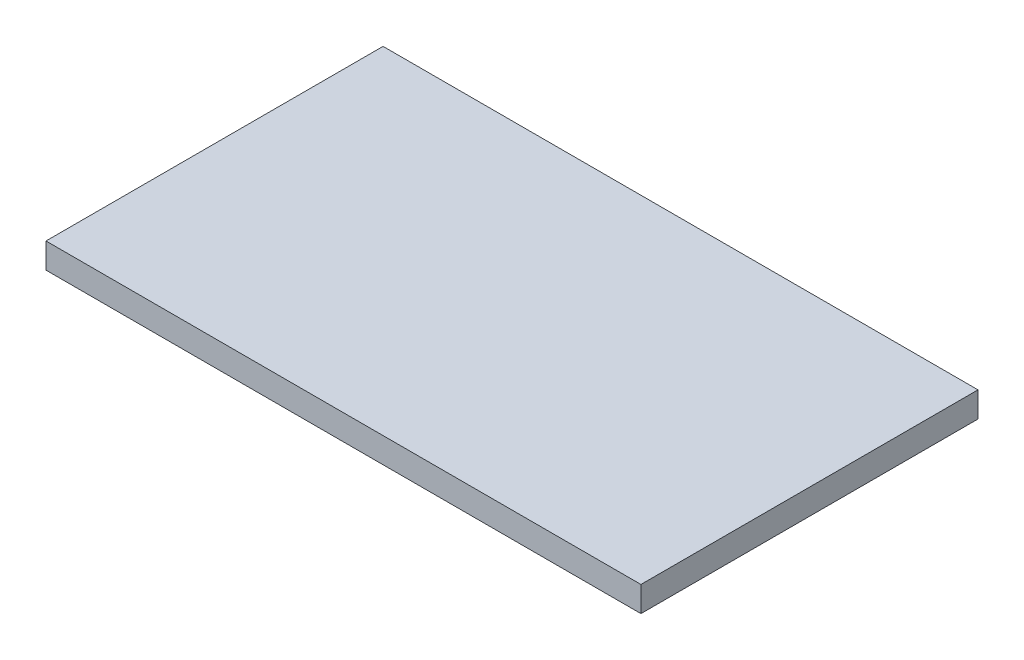
SolidWorks part; units mm, degrees
ref_plane "Front Plane" through (0, 0, 0) normal (0, 0, 1) x (1, 0, 0)
ref_plane "Top Plane" through (0, 0, 0) normal (0, 1, 0) x (1, 0, 0)
ref_plane "Right Plane" through (0, 0, 0) normal (1, 0, 0) x (0, 0, -1)
sketch "Sketch1" plane through (0, 0, 0) normal (0, 1, 0) x (1, 0, 0)
  line L0 (-36.882, 20.1438) -> (-36.882, -19.8562)
  line L1 (-36.882, -19.8562) -> (33.718, -19.8562)
  line L2 (33.718, -19.8562) -> (33.718, 20.1438)
  line L3 (33.718, 20.1438) -> (-36.882, 20.1438)
extrude "Boss-Extrude1" add sketch "Sketch1" along normal blind 3
